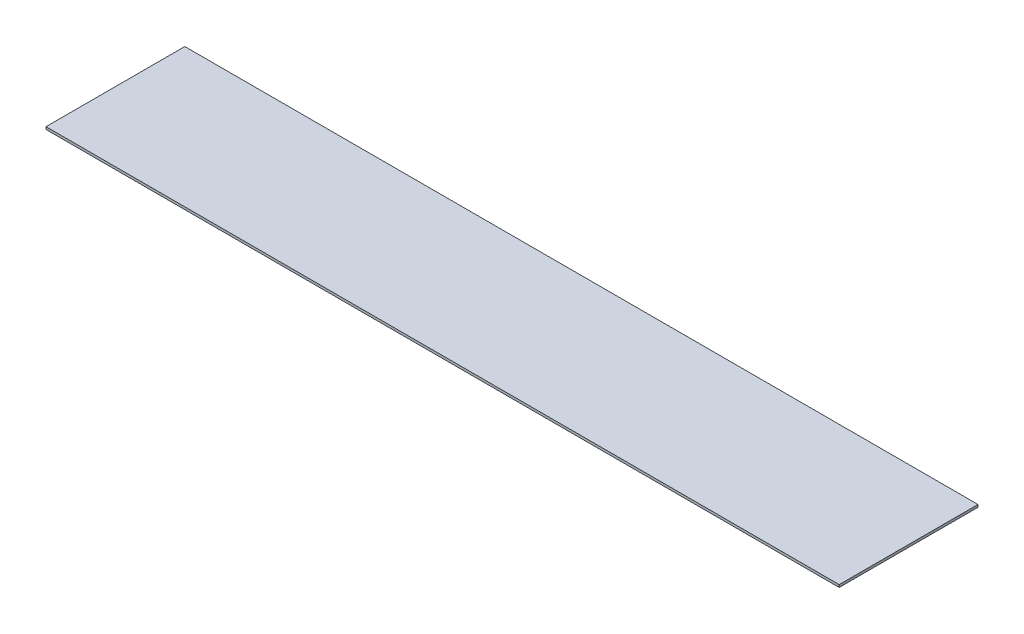
SolidWorks part; units mm, degrees
ref_plane "Front Plane" through (0, 0, 0) normal (0, 0, 1) x (1, 0, 0)
ref_plane "Top Plane" through (0, 0, 0) normal (0, 1, 0) x (1, 0, 0)
ref_plane "Right Plane" through (0, 0, 0) normal (1, 0, 0) x (0, 0, -1)
sketch "Sketch1" plane through (0, 0, 0) normal (0, 1, 0) x (1, 0, 0)
  line L1 (-254, -44.45) -> (254, -44.45)
  line L2 (-254, -44.45) -> (-254, 44.45)
  line L3 (-254, 44.45) -> (254, 44.45)
  line L4 (254, -44.45) -> (254, 44.45)
  line L5 (-254, -44.45) -> (254, 44.45) construction
  line L6 (-254, 44.45) -> (254, -44.45) construction
  point P0 (0, 0)
  dimension "D1" = 508
  dimension "D2" = 88.9
extrude "Boss-Extrude1" add sketch "Sketch1" along normal blind 1.5875
